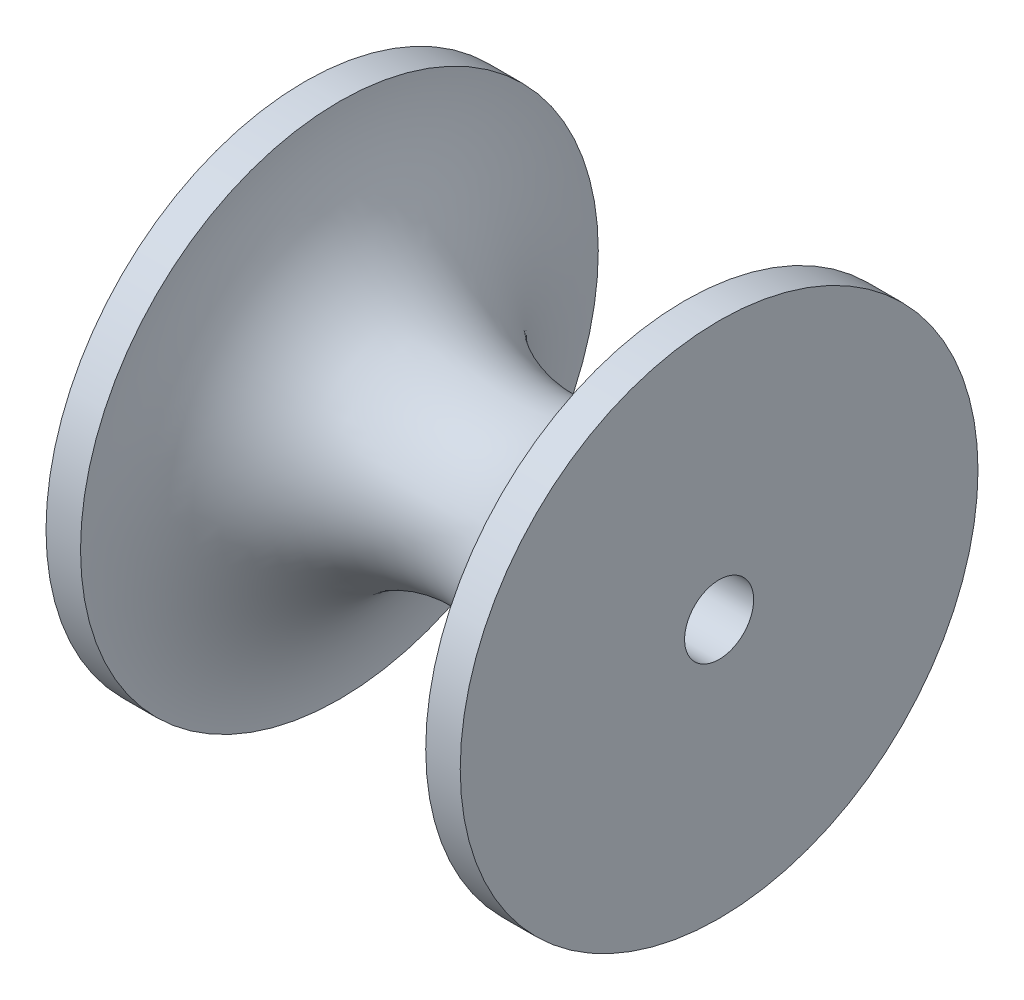
SolidWorks part; units mm, degrees
ref_plane "Front Plane" through (0, 0, 0) normal (0, 0, 1) x (1, 0, 0)
ref_plane "Top Plane" through (0, 0, 0) normal (0, 1, 0) x (1, 0, 0)
ref_plane "Right Plane" through (0, 0, 0) normal (1, 0, 0) x (0, 0, -1)
sketch "Sketch1" plane through (0, 0, 0) normal (0, 0, 1) x (1, 0, 0)
  line L3 (-10, -12.5) -> (10, -12.5)
  line L7 (10, 2.5) -> (12, 2.5)
  line L9 (10, -12.5) -> (12, -12.5)
  line L10 (12, 2.5) -> (12, -12.5)
  line L11 (-10, 2.5) -> (-12, 2.5)
  line L13 (-10, -12.5) -> (-12, -12.5)
  line L14 (-12, 2.5) -> (-12, -12.5)
  arc A0 (-10, 2.5) -> (10, 2.5) centre (0, 2.5) ccw
  point P0 (0, 0)
  dimension "D1" = 15
  dimension "D2" = 20
  dimension "D3" = 2
  dimension "D4" = 2
revolve "Revolve1" add sketch "Sketch1" angle 360 about L3
sketch "Sketch2" plane through (12, 0, 0) normal (1, 0, 0) x (0, 0, -1)
  line L0 (0, 2.5) -> (0, -27.5) construction
  circle A0 centre (0, -12.5) radius 15 construction
  circle A1 centre (0, -12.5) radius 2
  dimension "D1" = 4
extrude "Cut-Extrude1" cut sketch "Sketch2" against normal through all
